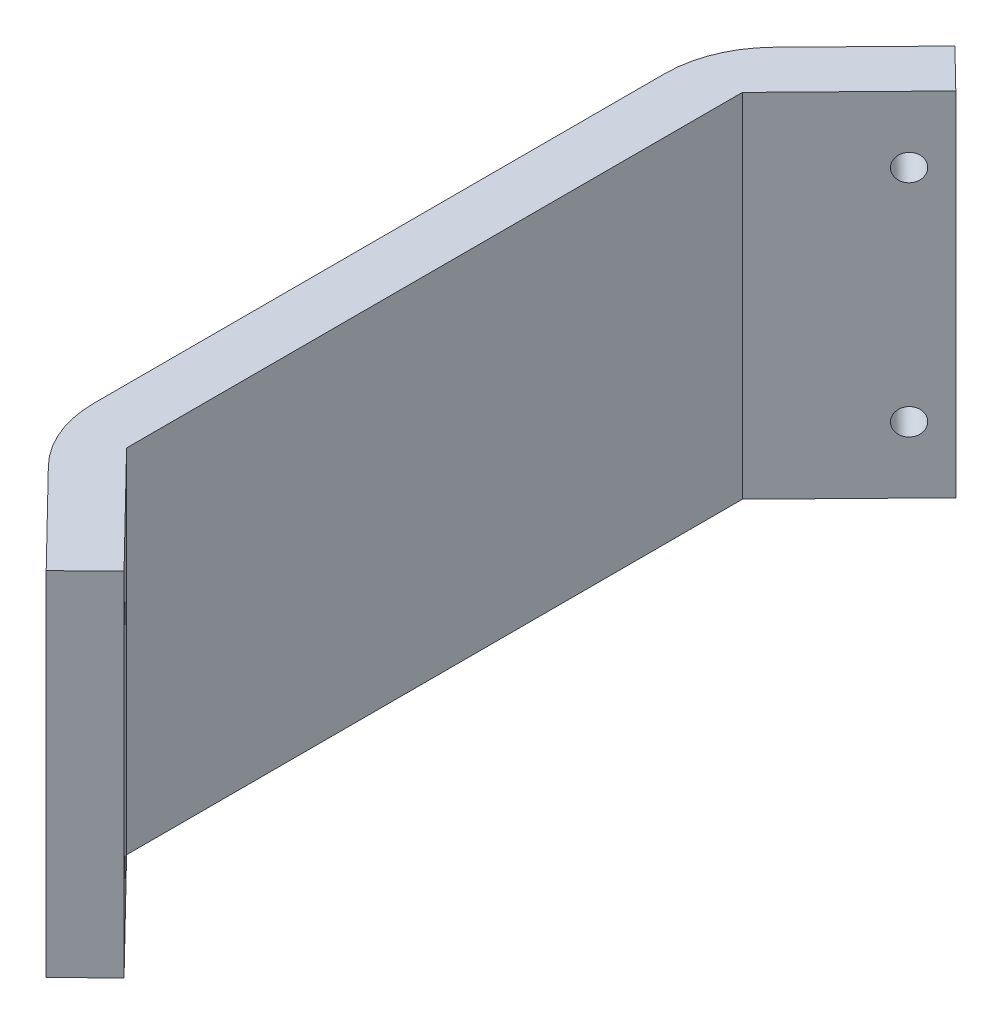
SolidWorks part; units mm, degrees
material "PEI"
ref_plane "Front Plane" through (0, 0, 0) normal (0, 0, 1) x (1, 0, 0)
ref_plane "Top Plane" through (0, 0, 0) normal (0, 1, 0) x (1, 0, 0)
ref_plane "Right Plane" through (0, 0, 0) normal (1, 0, 0) x (0, 0, -1)
sketch "Sketch1" plane through (0, 0, 0) normal (0, 1, 0) x (1, 0, 0)
  line L0 (0, 0) -> (0, 30)
  line L1 (0, 30) -> (83, 115)
  line L2 (0, 0) -> (18.2593, 0) construction
  line L3 (5, 27.9637) -> (5, -27.9637)
  line L5 (5, 27.9637) -> (83, 107.8432)
  line L6 (0, 0) -> (0.2825, 0) construction
  line L7 (5, 1.657) -> (5, 27.9637) construction
  line L8 (83, -115) -> (83, -107.8432)
  line L9 (83, 115) -> (83, 107.8432)
  line L10 (5, 27.9637) -> (86.5774, 111.5068) construction
  line L11 (5, -27.9637) -> (83, -107.8432)
  line L12 (0, -30) -> (83, -115)
  line L13 (0, 0) -> (0, -30)
  line L14 (5, 1.657) -> (5, 1.657) construction
  dimension "D1" = 30
  dimension "D2" = 83
  dimension "D4" = 85
  dimension "D3" = 5
extrude "Boss-Extrude1" add sketch "Sketch1" along normal blind 32
sketch "Sketch2" plane through (0, 32, 0) normal (0, 1, 0) x (1, 0, 0)
  line L0 (83, 115) -> (83, -115)
  line L1 (83, -115) -> (0, -30)
  line L2 (0, -30) -> (0, 30)
  line L3 (0, 30) -> (83, 115)
extrude "Boss-Extrude2" [suppressed] add sketch "Sketch2" along normal blind 5
fillet "Fillet1" radius 10 2 edges at (0, 16, -30) (0, 16, 30)
sketch "Sketch3" [suppressed] plane through (0, 37, 0) normal (0, 1, 0) x (1, 0, 0)
  line L0 (0, 25.9274) -> (0, -25.9274) construction
  line L1 (5, -30) -> (65, -30)
  line L2 (5, -30) -> (5, 30)
  line L3 (5, 30) -> (65, 30)
  line L4 (65, -30) -> (65, 30)
  line L5 (5, -30) -> (65, 30) construction
  line L6 (5, 30) -> (65, -30) construction
  point P0 (35, 0)
  dimension "D1" = 60
  dimension "D2" = 60
  dimension "D3" = 5
extrude "Cut-Extrude1" [suppressed] cut sketch "Sketch3" against normal through all
sketch "Sketch4" plane through (0, 32, 0) normal (0, 1, 0) x (1, 0, 0)
  line L4 (120.6904, -133.051) -> (-49.42, -133.051)
  line L6 (14.5774, -37.7719) -> (11, -41.2651)
  line L11 (83, -107.8432) -> (5, -27.9637) construction
  line L12 (2.8453, -32.9138) -> (83, -115) construction
  line L13 (14.5774, 37.7719) -> (11, 41.2651)
  line L14 (5, 27.9637) -> (83, 107.8432) construction
  line L15 (83, 115) -> (2.8453, 32.9138) construction
  line L16 (14.5774, -37.7719) -> (14.5774, 37.7719)
  line L17 (11, -41.2651) -> (0, -41.2651)
  line L18 (0, -41.2651) -> (0, 41.2651)
  line L19 (11, 41.2651) -> (0, 41.2651)
  line L20 (120.6904, -133.051) -> (120.6904, 124.9571)
  line L21 (120.6904, 124.9571) -> (-49.42, 124.9571)
  line L22 (-49.42, -133.051) -> (-49.42, 124.9571)
  dimension "D1" = 11
extrude "Cut-Extrude2" cut sketch "Sketch4" against normal through all
sketch "Sketch6" plane through (-14.9957, 0, -14.6429) normal (-0.7155, 0, -0.6986) x (-0.6986, 0, 0.7155)
  line L0 (-35.7778, 16) -> (49964.2222, 16) construction
  line L1 (-37.2091, 0) -> (-37.2091, 32) construction
  circle A0 centre (-34.2091, 26) radius 1.2
  circle A1 centre (-34.2091, 6) radius 1.2
  point P4 (-37.2091, 16)
  dimension "D1" = 2.4
  dimension "D2" = 3
  dimension "D3" = 10
extrude "Cut-Extrude3" cut sketch "Sketch6" against normal through all
sketch "Sketch7" plane through (-14.9957, 0, 14.6429) normal (-0.7155, 0, 0.6986) x (0.6986, 0, 0.7155)
  line L0 (35.7778, 16) -> (-49964.2222, 16) construction
  line L1 (37.2091, 0) -> (37.2091, 32) construction
  circle A0 centre (34.2091, 26) radius 1.2
  circle A1 centre (34.2091, 6) radius 1.2
  point P4 (37.2091, 16)
  dimension "D1" = 2.4
  dimension "D2" = 3
  dimension "D3" = 10
extrude "Cut-Extrude4" cut sketch "Sketch7" against normal through all
